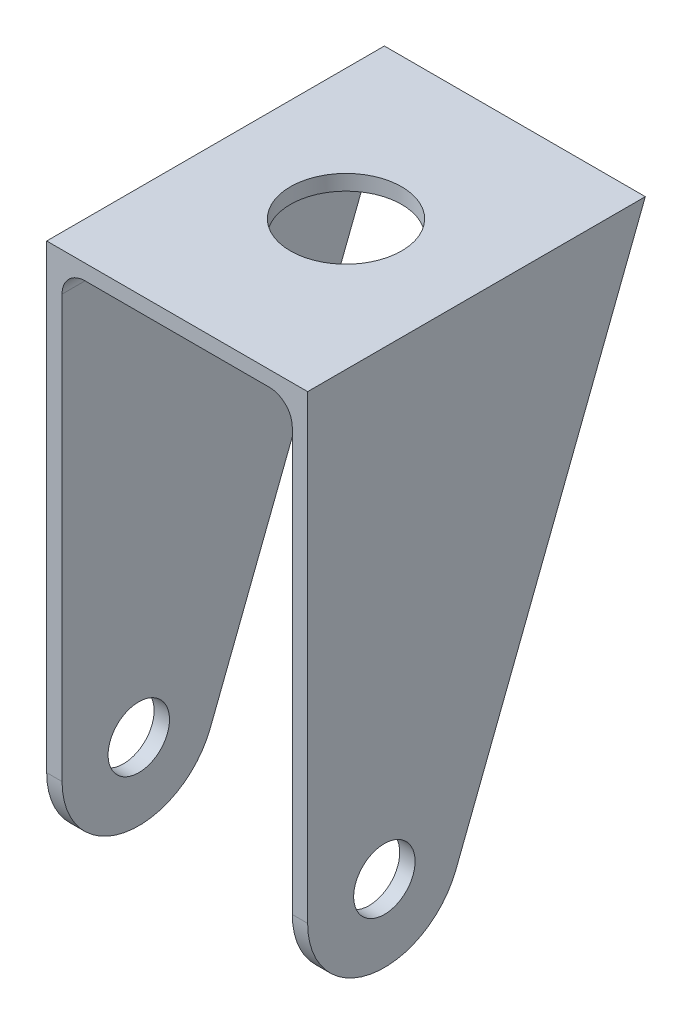
SolidWorks part; units mm, degrees
ref_plane "Alzado" through (0, 0, 0) normal (0, 0, 1) x (1, 0, 0)
ref_plane "Planta" through (0, 0, 0) normal (0, 1, 0) x (1, 0, 0)
ref_plane "Vista lateral" through (0, 0, 0) normal (1, 0, 0) x (0, 0, -1)
ref_plane "Plano1" through (17, 0, 0) normal (1, 0, 0) x (0, 0, -1)
sketch "Croquis1" plane through (17, 0, 0) normal (1, 0, 0) x (0, 0, -1)
  line L0 (-10, 0) -> (-10, 60)
  line L1 (-10, 60) -> (34, 60)
  line L2 (34, 60) -> (9.3232, -3.6165)
  circle A0 centre (0, 0) radius 4
  arc A1 (-10, 0) -> (9.3232, -3.6165) centre (0, 0) ccw
  dimension "D1" = 8
  dimension "D2" = 20
  dimension "D3" = 44
  dimension "D4" = 60
extrude "Saliente-Extruir1" add sketch "Croquis1" against normal blind 34
sketch "Croquis3" plane through (0, 0, 0) normal (0, 0, 1) x (1, 0, 0)
  line L0 (-15, -10) -> (15, -10)
  line L1 (0, 0) -> (0, -10) construction
  line L2 (-17, -10) -> (17, -10) construction
  line L3 (-15, -10) -> (-15, 55)
  line L4 (-12, 58) -> (12, 58)
  line L5 (15, 55) -> (15, -10)
  line L6 (-15, 60) -> (15, 60) construction
  line L7 (-17, 60) -> (17, 60) construction
  arc A0 (15, 55) -> (12, 58) centre (12, 55) ccw
  arc A1 (-12, 58) -> (-15, 55) centre (-12, 55) ccw
  point P7 (0, -10)
  dimension "D3" = 3
  dimension "D1" = 30
  dimension "D2" = 2
extrude "Cortar-Extruir1" cut sketch "Croquis3" against normal up to next and the other way up to next
sketch "Croquis4" plane through (0, 60, 0) normal (0, 1, 0) x (1, 0, 0)
  line L0 (-17, -10) -> (0, -10) construction
  line L1 (-17, -10) -> (17, -10) construction
  line L2 (0, -10) -> (0, 12) construction
  circle A0 centre (0, 12) radius 7.25
  dimension "D2" = 14.5
  dimension "D1" = 22
extrude "Cortar-Extruir2" cut sketch "Croquis4" against normal up to next
